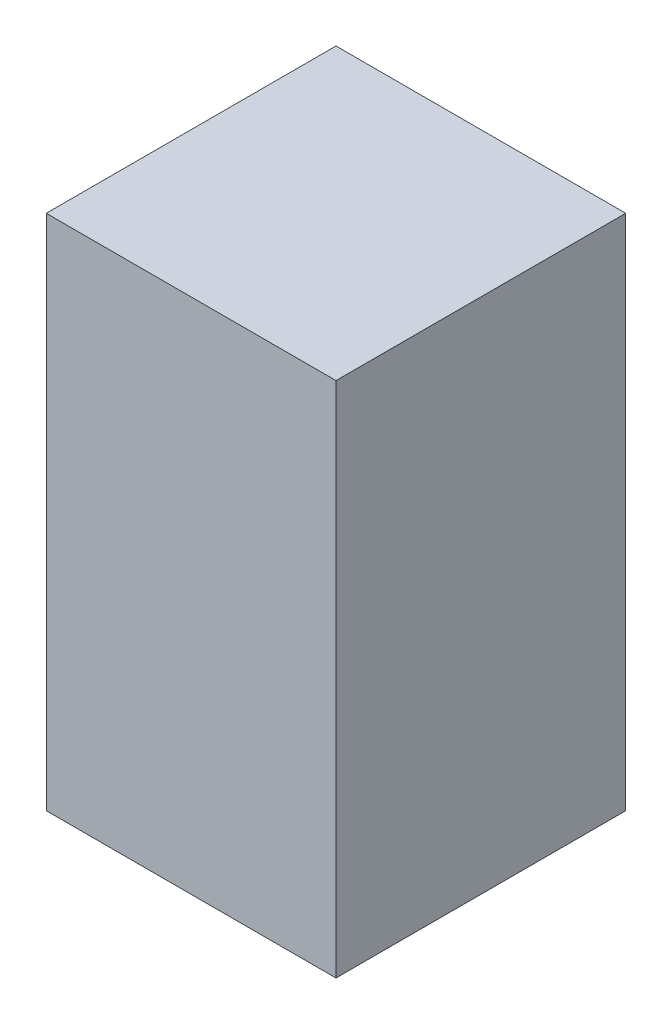
SolidWorks part; units mm, degrees
ref_plane "Front Plane" through (0, 0, 0) normal (0, 0, 1) x (1, 0, 0)
ref_plane "Top Plane" through (0, 0, 0) normal (0, 1, 0) x (1, 0, 0)
ref_plane "Right Plane" through (0, 0, 0) normal (1, 0, 0) x (0, 0, -1)
sketch "Sketch3" plane through (0, 0, 0) normal (1, 0, 0) x (0, 0, -1)
  line L0 (0, 0) -> (28, 0)
  line L1 (28, 0) -> (28, 50)
  line L2 (28, 50) -> (0, 50)
  line L3 (0, 50) -> (0, 0)
  dimension "D1" = 28
  dimension "D2" = 50
extrude "Boss-Extrude1" add sketch "Sketch3" along normal mid plane 28
sketch "Sketch6" plane through (0, 0, 0) normal (0, -1, 0) x (-1, 0, 0)
  line L0 (-14, 28) -> (14, 28) construction
  circle A0 centre (0, 14) radius 12.5
  dimension "D1" = 25
  dimension "D2" = 14
extrude "Cut-Extrude1" cut sketch "Sketch6" against normal blind 40
